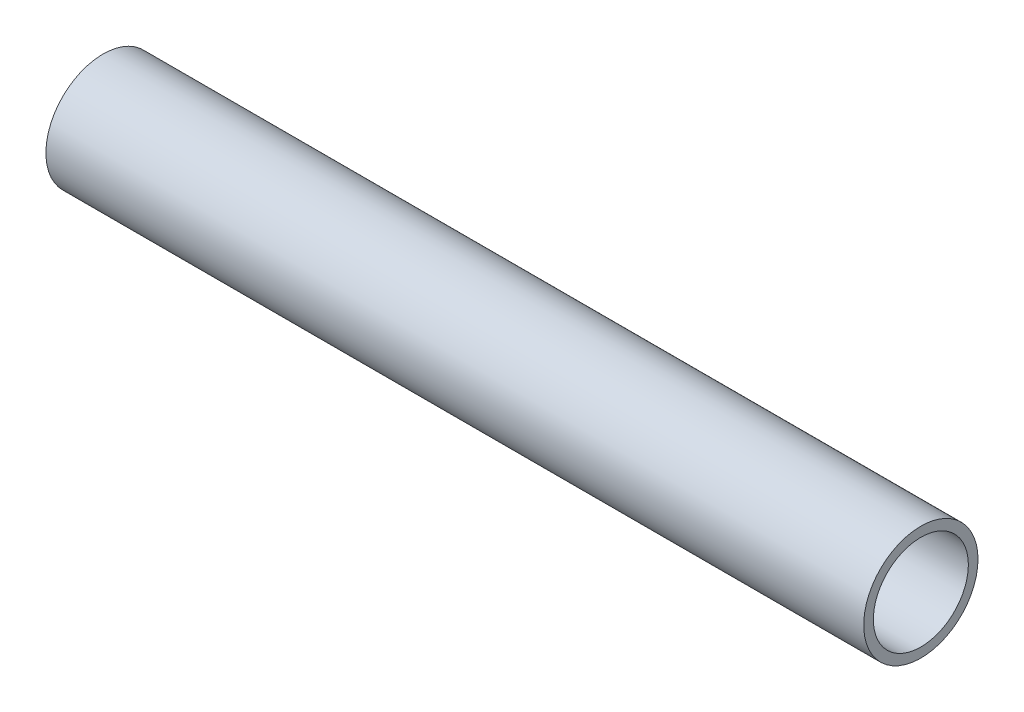
SolidWorks part; units mm, degrees
material "6061-T6 (SS)"
ref_plane "Front Plane" through (0, 0, 0) normal (0, 0, 1) x (1, 0, 0)
ref_plane "Top Plane" through (0, 0, 0) normal (0, 1, 0) x (1, 0, 0)
ref_plane "Right Plane" through (0, 0, 0) normal (1, 0, 0) x (0, 0, -1)
sketch "Sketch1" plane through (0, 0, 0) normal (1, 0, 0) x (0, 0, -1)
  circle A0 centre (0, 0) radius 21.082
  circle A1 centre (0, 0) radius 17.526
  dimension "D1" = 42.164
  dimension "D2" = 35.052
extrude "Boss-Extrude1" add sketch "Sketch1" along normal blind 127 and the other way blind 174.625
sketch "Sketch2" plane through (0, 0, 0) normal (0, 0, 1) x (1, 0, 0)
  line L0 (-174.625, 21.082) -> (-174.625, -21.082) construction
  circle A0 centre (-98.425, 0) radius 3.175
  circle A1 centre (-149.225, 0) radius 3.175
  dimension "D1" = 6.35
  dimension "D2" = 25.4
  dimension "D3" = 50.8
extrude "Cut-Extrude1" cut sketch "Sketch2" against normal through all
